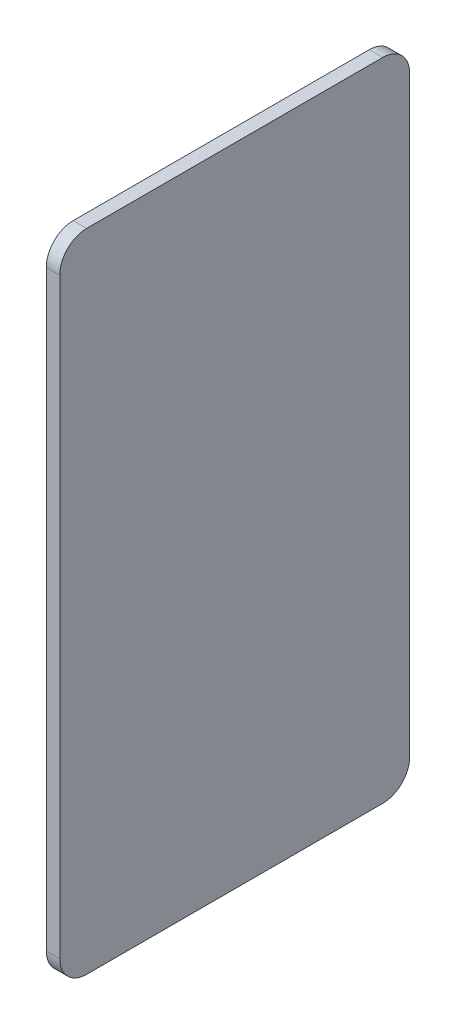
SolidWorks part; units mm, degrees
material "Acrylic (Medium-high impact)"
ref_plane "Front Plane" through (0, 0, 0) normal (0, 0, 1) x (1, 0, 0)
ref_plane "Top Plane" through (0, 0, 0) normal (0, 1, 0) x (1, 0, 0)
ref_plane "Right Plane" through (0, 0, 0) normal (1, 0, 0) x (0, 0, -1)
sketch "Sketch1" plane through (158.5173, 0, 0) normal (1, 0, 0) x (0, 0, -1)
  line L1 (152.7385, -131.2288) -> (22.7385, -131.2288)
  line L2 (152.7385, -131.2288) -> (152.7385, 108.7712)
  line L3 (152.7385, 108.7712) -> (22.7385, 108.7712)
  line L4 (22.7385, -131.2288) -> (22.7385, 108.7712)
extrude "Boss-Extrude1" add sketch "Sketch1" against normal blind 5
fillet "Fillet1" radius 10 4 edges at (156.0173, -131.2288, -22.7385) (156.0173, -131.2288, -152.7385) (156.0173, 108.7712, -22.7385) (156.0173, 108.7712, -152.7385)
